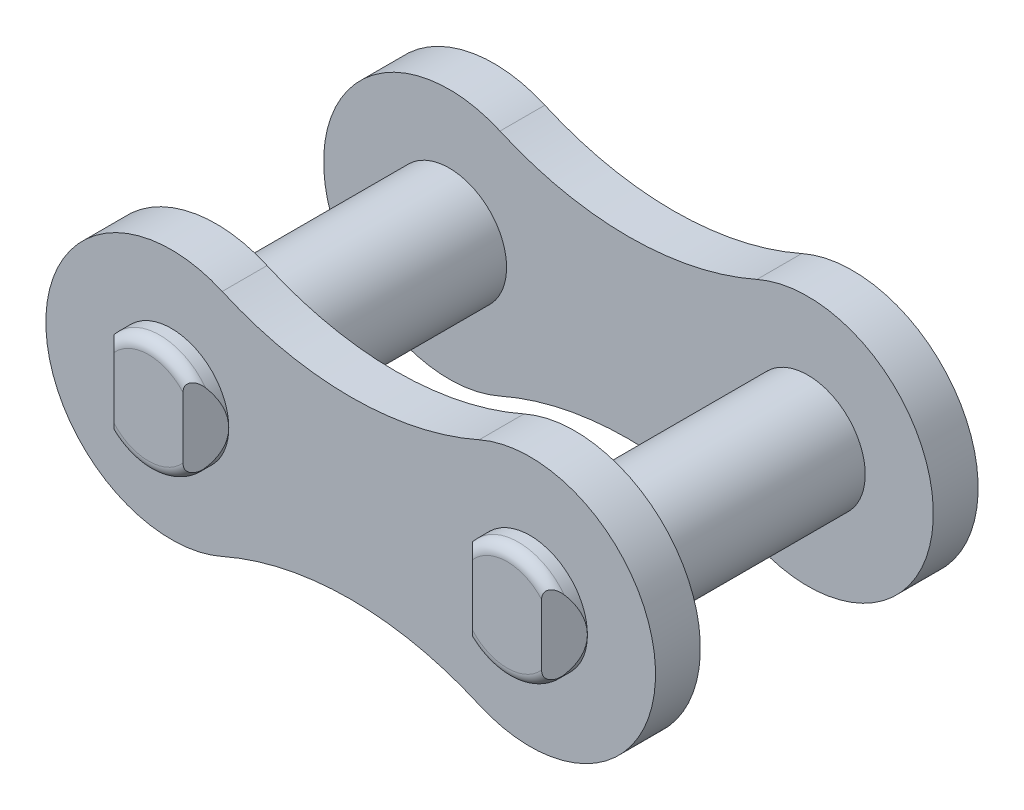
SolidWorks part; units mm, degrees
material "AISI 4130 Steel, normalized at 870C"
ref_plane "Front Plane" through (0, 0, 0) normal (0, 0, 1) x (1, 0, 0)
ref_plane "Top Plane" through (0, 0, 0) normal (0, 1, 0) x (1, 0, 0)
ref_plane "Right Plane" through (0, 0, 0) normal (1, 0, 0) x (0, 0, -1)
ref_plane "Plane1" through (7.9375, 0, 0) normal (1, 0, 0) x (0, 0, -1)
sketch "Sketch1" plane through (0, 0, 0) normal (0, 1, 0) x (1, 0, 0)
  line L0 (0, -8.1534) -> (-2.04, -8.1534)
  line L1 (0, 8.1534) -> (-2.04, 8.1534)
  line L4 (-2.54, 7.6534) -> (-2.54, -7.6534)
  line L7 (0, -8.1534) -> (0, 8.1534)
  arc A1 (-2.04, 8.1534) -> (-2.54, 7.6534) centre (-2.04, 7.6534) ccw
  arc A3 (-2.04, -8.1534) -> (-2.54, -7.6534) centre (-2.04, -7.6534) cw
  point P0 (0, 0)
  dimension "D3" = 0.5
  dimension "D4" = 0.5
  dimension "D1" = 2.54
  dimension "D2" = 16.3068
revolve "Revolve1" add sketch "Sketch1" angle 360 about L7
sketch "Sketch2" plane through (0, 0, 0) normal (0, 0, 1) x (1, 0, 0)
  line L0 (0, 0) -> (6.5925, 0) construction
  line L1 (1.6358, 5.08) -> (13.8975, 5.08) construction
  arc A0 (2.2507, 5.08) -> (2.2507, -5.08) centre (0, 0) ccw
  arc A1 (13.6243, -5.08) -> (13.6243, 5.08) centre (15.875, 0) ccw
  circle A2 centre (0, 0) radius 5.08 construction
  circle A3 centre (0, 0) radius 2.54
  arc A4 (2.2507, 5.08) -> (13.6243, 5.08) centre (7.9375, 17.9158) ccw
  circle A5 centre (15.875, 0) radius 2.54
  arc A7 (2.2507, -5.08) -> (13.6243, -5.08) centre (7.9375, -17.9158) cw
  dimension "D1" = 11.1125
  dimension "D2" = 10.16
  dimension "D3" = 5.08
  dimension "D4" = 15.875
extrude "Boss-Extrude2" add sketch "Sketch2" along normal blind 1.9844 from offset 5.1562 separate body
sketch "Sketch6" plane through (0, 0, 0) normal (0, 1, 0) x (1, 0, 0)
  line L0 (0, 0) -> (0, 4.1737) construction
  line L1 (1.5272, -8.1534) -> (2.54, -7.1406)
  line L2 (2.54, -7.1406) -> (2.54, -9.1534)
  line L6 (-2.54, -7.1406) -> (-2.54, -9.1534)
  line L7 (-1.5272, -8.1534) -> (-2.54, -7.1406)
  line L8 (1.5272, -8.1534) -> (-1.5272, -8.1534)
  line L9 (-2.54, -9.1534) -> (2.54, -9.1534)
  line L12 (0, 0) -> (-3.2406, 0) construction
  line L13 (-2.54, 9.1534) -> (2.54, 9.1534)
  line L14 (1.5272, 8.1534) -> (-1.5272, 8.1534)
  line L15 (-1.5272, 8.1534) -> (-2.54, 7.1406)
  line L16 (-2.54, 7.1406) -> (-2.54, 9.1534)
  line L17 (2.54, 7.1406) -> (2.54, 9.1534)
  line L18 (1.5272, 8.1534) -> (2.54, 7.1406)
  line L19 (-2.04, -8.1534) -> (2.04, -8.1534) construction
  dimension "D1" = 45
  dimension "D2" = 1
extrude "Cut-Extrude1" cut sketch "Sketch6" against normal through all and the other way through all
mirror "Mirror5" about plane through (7.9375, 0, 0) normal (1, 0, 0) of bodies 119
mirror "Mirror6" about plane through (0, 0, 0) normal (0, 0, 1) of bodies 110
